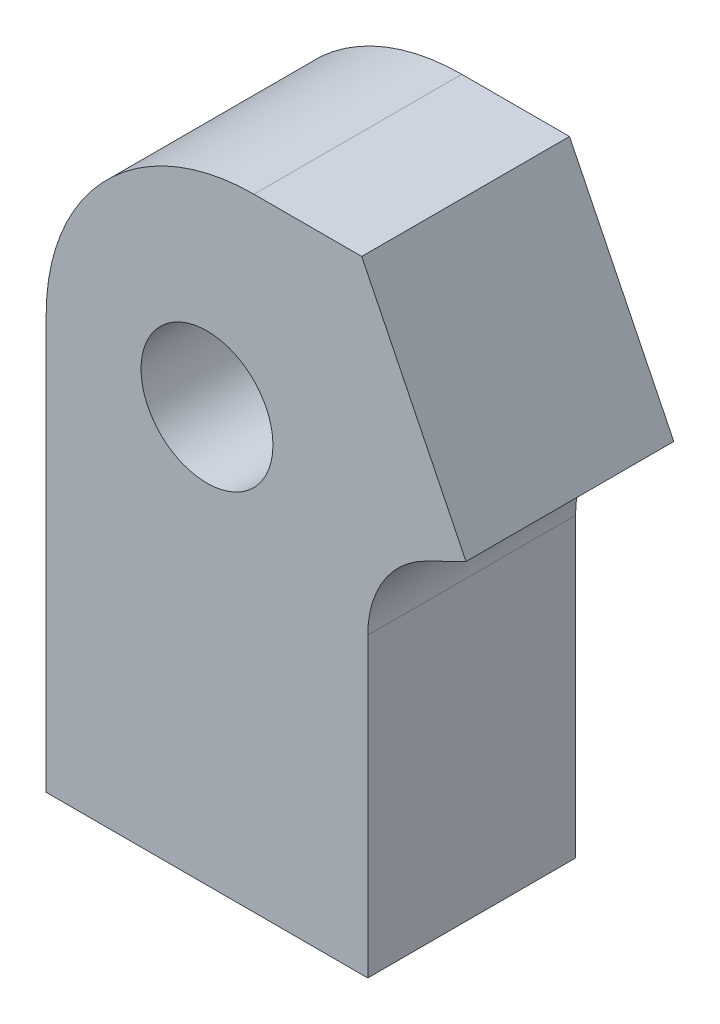
SolidWorks part; units mm, degrees
ref_plane "Front Plane" through (0, 0, 0) normal (0, 0, 1) x (1, 0, 0)
ref_plane "Top Plane" through (0, 0, 0) normal (0, 1, 0) x (1, 0, 0)
ref_plane "Right Plane" through (0, 0, 0) normal (1, 0, 0) x (0, 0, -1)
sketch "Sketch1" plane through (0, 0, 0) normal (0, 0, 1) x (1, 0, 0)
  line L0 (59.8213, 0) -> (-61.3819, 0) construction
  line L1 (-47.4644, 0) -> (-47.4644, 19.93)
  line L2 (-37.4644, 29.93) -> (-32.2788, 29.93)
  line L3 (-32.2788, 29.93) -> (-29.7691, 24.8281)
  line L4 (-39.7264, 19.93) -> (1.0536, 39.99) construction
  line L5 (-31.9883, 0) -> (-31.9883, 14.2873)
  line L6 (-31.9883, 0) -> (-47.4644, 0)
  line L7 (-29.7691, 24.8281) -> (-27.2594, 19.7262)
  line L8 (-39.7264, 19.93) -> (12.4792, 19.93) construction
  line L10 (-31.9883, 10.7369) -> (-39.7264, 10.7369) construction
  line L11 (-39.7264, 10.7369) -> (-47.4644, 10.7369) construction
  line L12 (-39.7264, 19.93) -> (-39.7264, 10.7369) construction
  line L13 (-29.1953, 18.7739) -> (-27.2594, 19.7262)
  circle A0 centre (1.0536, 39.99) radius 3.175 construction
  circle A1 centre (-39.7264, 19.93) radius 3.175
  circle A2 centre (1.0536, 39.99) radius 29.35 construction
  arc A3 (-37.4644, 29.93) -> (-47.4644, 19.93) centre (-37.4644, 19.93) ccw
  circle A4 centre (1.0536, 39.99) radius 34.35 construction
  arc A6 (-31.9883, 14.2873) -> (-29.1953, 18.7739) centre (-26.9883, 14.2873) cw
  dimension "D3" = 6.35
  dimension "D4" = 6.35
  dimension "D5" = 58.7
  dimension "D7" = 10
  dimension "D8" = 90
  dimension "D11" = 5
  dimension "D13" = 5
  dimension "D1" = 19.93
  dimension "D2" = 40.78
  dimension "D6" = 90
  dimension "D9" = 20.06
  dimension "D10" = 90
  dimension "D12" = 10
extrude "Boss-Extrude1" add sketch "Sketch1" along normal blind 10
